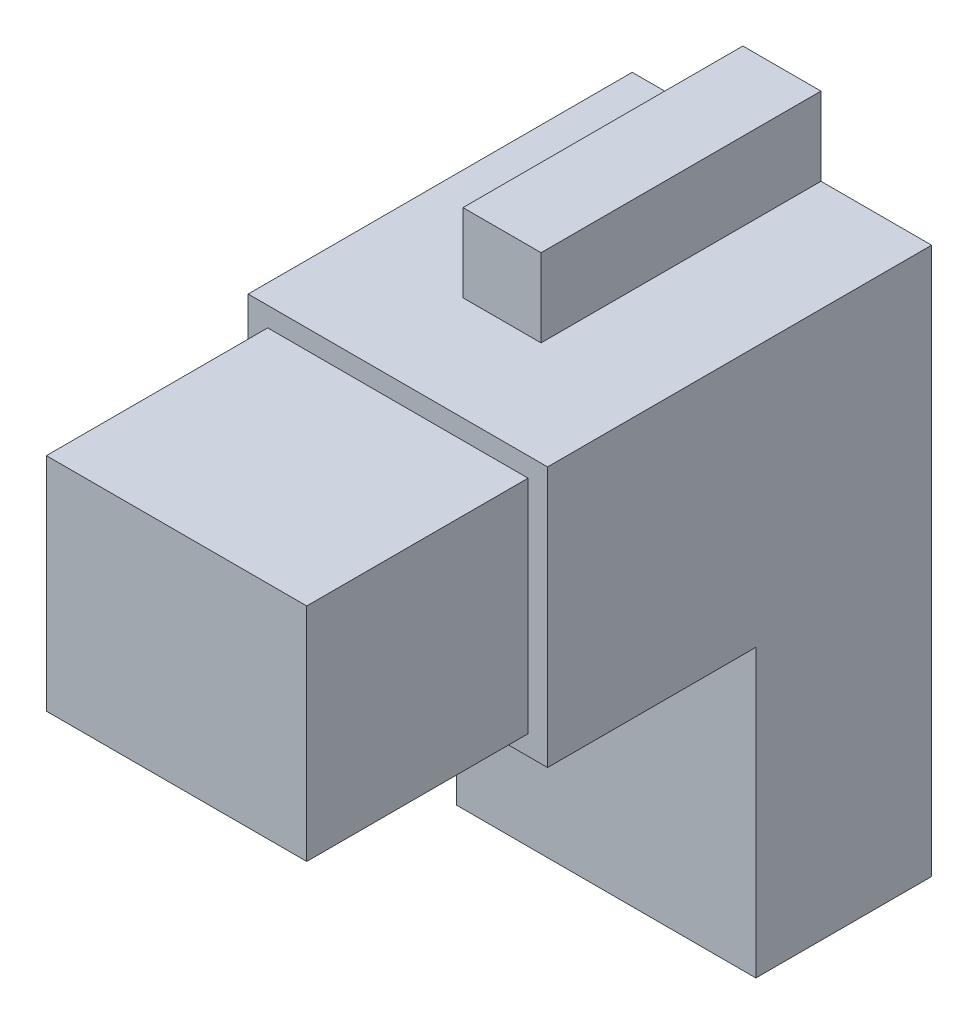
SolidWorks part; units mm, degrees
ref_plane "Alzado" through (0, 0, 0) normal (0, 0, 1) x (1, 0, 0)
ref_plane "Planta" through (0, 0, 0) normal (0, 1, 0) x (1, 0, 0)
ref_plane "Vista lateral" through (0, 0, 0) normal (1, 0, 0) x (0, 0, -1)
sketch "Croquis1" plane through (0, 0, 0) normal (0, 0, 1) x (1, 0, 0)
  line L0 (-9.9588, -27.1247) -> (13.0412, -27.1247)
  line L1 (13.0412, -27.1247) -> (13.0412, 14.8753)
  line L2 (-9.9588, 14.8753) -> (-1.4588, 14.8753)
  line L3 (-9.9588, 14.8753) -> (-9.9588, -27.1247)
  line L4 (4.5412, 14.8753) -> (13.0412, 14.8753)
  line L5 (4.5412, 20.8753) -> (-1.4588, 20.8753)
  line L6 (4.5412, 14.8753) -> (4.5412, 20.8753)
  line L8 (-1.4588, 20.8753) -> (-1.4588, 14.8753)
extrude "Saliente-Extruir1" add sketch "Croquis1" along normal blind 13.5
sketch "Croquis2" plane through (0, 0, 0) normal (0, 0, -1) x (-1, 0, 0)
  line L0 (-13.0412, -27.1247) -> (-13.0412, 14.8753) construction
  line L1 (9.9588, -27.1247) -> (-13.0412, -27.1247) construction
  circle A0 centre (-1.5412, -16.1247) radius 2
  point P4 (-1.5412, -27.1247)
  dimension "D1" = 4
  dimension "D2" = 11.5
  dimension "D3" = 11
extrude "Saliente-Extruir2" add sketch "Croquis2" along normal blind 1
sketch "Croquis6" plane through (0, 0, 13.5) normal (0, 0, 1) x (1, 0, 0)
  line L0 (13.0412, 14.8753) -> (4.5412, 14.8753) construction
  line L1 (-1.4588, -5.1247) -> (4.5412, -5.1247)
  line L2 (-1.4588, -5.1247) -> (-1.4588, -11.1247)
  line L3 (-1.4588, -11.1247) -> (4.5412, -11.1247)
  line L4 (4.5412, -5.1247) -> (4.5412, -11.1247)
  line L5 (13.0412, -27.1247) -> (13.0412, 14.8753) construction
  dimension "D1" = 6
  dimension "D2" = 6
  dimension "D3" = 20
  dimension "D4" = 8.5
extrude "Saliente-Extruir3" add sketch "Croquis6" along normal blind 8
sketch "Croquis7" plane through (0, 0, 13.5) normal (0, 0, 1) x (1, 0, 0)
  line L0 (-1.4588, 14.8753) -> (4.5412, 14.8753)
  line L1 (4.5412, 14.8753) -> (4.5412, 20.8753)
  line L2 (4.5412, 20.8753) -> (-1.4588, 20.8753)
  line L3 (-1.4588, 20.8753) -> (-1.4588, 14.8753)
extrude "Saliente-Extruir4" add sketch "Croquis7" along normal blind 8
sketch "Croquis8" plane through (0, 0, 13.5) normal (0, 0, 1) x (1, 0, 0)
  line L0 (-9.9588, 14.8753) -> (13.0412, 14.8753)
  line L1 (13.0412, 14.8753) -> (13.0412, -5.1247)
  line L2 (13.0412, -27.1247) -> (13.0412, 14.8753) construction
  line L3 (13.0412, -5.1247) -> (-9.9588, -5.1247)
  line L4 (-9.9588, 14.8753) -> (-9.9588, -27.1247) construction
  line L5 (-9.9588, -5.1247) -> (-9.9588, 14.8753)
extrude "Saliente-Extruir5" add sketch "Croquis8" along normal blind 16
sketch "Croquis9" plane through (0, 0, 29.5) normal (0, 0, 1) x (1, 0, 0)
  line L0 (-8.4588, 13.3753) -> (11.5412, 13.3753)
  line L1 (11.5412, 13.3753) -> (11.5412, -3.6247)
  line L2 (11.5412, -3.6247) -> (-8.4588, -3.6247)
  line L3 (-8.4588, -3.6247) -> (-8.4588, 13.3753)
  line L4 (-9.9588, 14.8753) -> (-9.9588, -5.1247) construction
  line L6 (13.0412, 14.8753) -> (-9.9588, 14.8753) construction
  line L7 (-9.9588, -5.1247) -> (13.0412, -5.1247) construction
  dimension "D1" = 20
  dimension "D2" = 1.5
  dimension "D3" = 1.5
  dimension "D4" = 1.5
extrude "Saliente-Extruir6" add sketch "Croquis9" along normal blind 17 contours L0 L1 L2 L3
